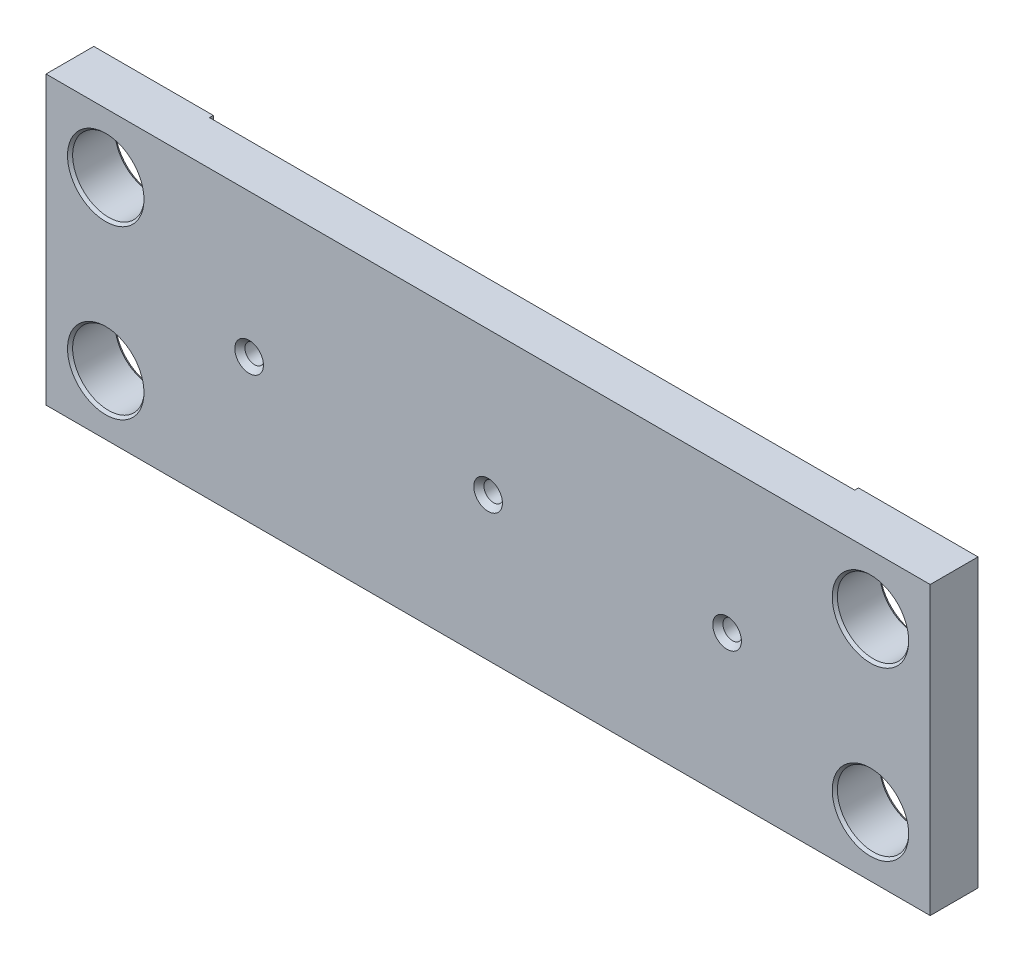
SolidWorks part; units mm, degrees
material "AISI 1018 Steel, Cold Rolled"
ref_plane "Front" through (0, 0, 0) normal (0, 0, 1) x (1, 0, 0)
ref_plane "Top" through (0, 0, 0) normal (0, 1, 0) x (1, 0, 0)
ref_plane "Right" through (0, 0, 0) normal (1, 0, 0) x (0, 0, -1)
sketch "Sketch1" plane through (0, 0, 0) normal (0, 0, 1) x (1, 0, 0)
  line L0 (0, 38.1) -> (0, -38.1) construction
  line L1 (-117.475, 38.1) -> (117.475, 38.1)
  line L2 (-117.475, 38.1) -> (-117.475, -38.1)
  line L3 (-117.475, -38.1) -> (117.475, -38.1)
  line L4 (117.475, 38.1) -> (117.475, -38.1)
  dimension "D1" = 234.95
  dimension "D2" = 76.2
extrude "Extrude1" add sketch "Sketch1" along normal blind 12.7
hole_wizard "1/2 Clearance Hole1" positions "Sketch3" profile "Sketch2" hole size "1/2" standard "Ansi Inch" end condition up to next
sketch "Sketch3" plane through (0, 0, 12.7) normal (0, 0, 1) x (1, 0, 0)
  line L0 (-101.6, 22.225) -> (-101.6, -22.225) construction
  line L3 (101.6, 22.225) -> (101.6, -22.225) construction
  line L6 (101.6, 0) -> (-101.6, 0) construction
  point P0 (-101.6, 22.225)
  point P1 (-101.6, -22.225)
  point P3 (101.6, 22.225)
  point P5 (101.6, -22.225)
  dimension "D1" = 203.2
  dimension "D2" = 44.45
sketch "Sketch2" plane through (-101.6, 22.225, 12.7) normal (1, 0, 0) x (0, -1, 0)
  line L0 (0, 0) -> (0, 12.7)
  line L1 (0, 12.7) -> (10.16, 12.7)
  line L2 (9.525, 11.9695) -> (9.525, 0.7305)
  line L3 (9.525, 0.7305) -> (10.16, 0)
  line L5 (10.16, 0) -> (0, 0)
  line L6 (-9.525, 0.7305) -> (-10.16, 0) construction
  line L7 (10.16, 12.7) -> (9.525, 11.9695)
  line L8 (-10.16, 12.7) -> (-9.525, 11.9695) construction
  line L11 (0, -6.35) -> (0, 107.95) construction
  dimension "Thru Hole Dia." = 19.05
  dimension "Thru Hole Depth" = 12.7
  dimension "Near C'Sink Dia." = 20.32
  dimension "Near C'Sink Angle" = 82
  dimension "Far C'Sink Dia." = 20.32
  dimension "Far C'Sink Angle" = 82
sketch "Sketch6" plane through (0, 0, 0) normal (0, 0, -1) x (-1, 0, 0)
  line L0 (-117.475, 38.1) -> (117.475, 38.1) construction
  line L1 (-85.725, 38.1) -> (85.725, 38.1)
  line L2 (-85.725, 38.1) -> (-85.725, -38.1)
  line L3 (-85.725, -38.1) -> (85.725, -38.1)
  line L4 (85.725, 38.1) -> (85.725, -38.1)
  line L5 (117.475, -38.1) -> (-117.475, -38.1) construction
  line L6 (-117.475, -38.1) -> (-117.475, 38.1) construction
  point P8 (0, 38.1)
  dimension "D1" = 31.75
extrude "Cut-Extrude1" cut sketch "Sketch6" against normal blind 1.016
hole_wizard "1/4-20 Tapped Hole1" positions "Sketch5" profile "Sketch4" tap size "1/4-20" standard "Ansi Inch" end condition up to next
sketch "Sketch5" plane through (0, 0, 12.7) normal (0, 0, 1) x (1, 0, 0)
  line L0 (63.5, 0) -> (-63.5, 0) construction
  point P0 (-63.5, 0)
  point P1 (0, 0)
  point P4 (63.5, 0)
  dimension "D1" = 127
cosmetic thread "Hole Thread1" parameters "D2"=6.35
cosmetic thread "Hole Thread2" parameters "D2"=6.35
cosmetic thread "Hole Thread3" parameters "D2"=6.35
sketch "Sketch4" plane through (-63.5, 0, 12.7) normal (1, 0, 0) x (0, -1, 0)
  line L0 (0, 0) -> (0, 11.684)
  line L1 (0, 11.684) -> (3.81, 11.684)
  line L2 (2.5527, 10.2376) -> (2.5527, 1.4464)
  line L3 (2.5527, 1.4464) -> (3.81, 0)
  line L5 (3.81, 0) -> (0, 0)
  line L6 (-2.5527, 1.4464) -> (-3.81, 0) construction
  line L7 (3.81, 11.684) -> (2.5527, 10.2376)
  line L8 (-3.81, 11.684) -> (-2.5527, 10.2376) construction
  line L11 (0, -6.35) -> (0, 107.95) construction
  dimension "Thru Tap Drill Dia." = 5.1054
  dimension "Thru Tap Drill Depth" = 11.684
  dimension "Near C'Sink Dia." = 7.62
  dimension "Near C'Sink Angle" = 82
  dimension "Far C'Sink Dia." = 7.62
  dimension "Far C'Sink Angle" = 82
